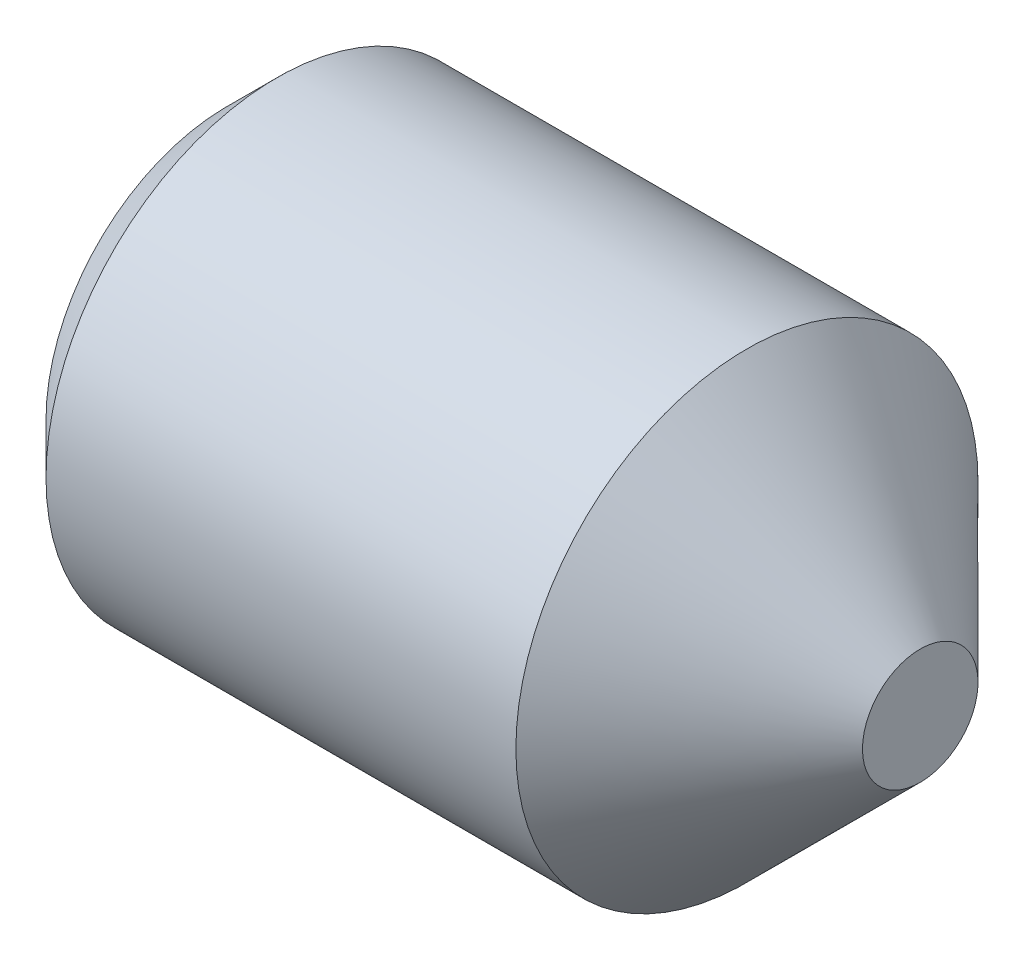
SolidWorks part; units mm, degrees
ref_plane "Front" through (0, 0, 0) normal (0, 0, 1) x (1, 0, 0)
ref_plane "Top" through (0, 0, 0) normal (0, 1, 0) x (1, 0, 0)
ref_plane "Right" through (0, 0, 0) normal (1, 0, 0) x (0, 0, -1)
sketch "Sketch1" plane through (0, 0, 0) normal (0, 0, 1) x (1, 0, 0)
  line L0 (0, 0) -> (3, 0)
  line L1 (3, 0) -> (3, 0.25)
  line L2 (3, 0.25) -> (2.25, 1)
  line L3 (2.25, 1) -> (0.2165, 1)
  line L4 (0.2165, 1) -> (0, 0.7835)
  line L5 (0, 0.7835) -> (0, 0)
  line L6 (-14.7741, 0) -> (12.5137, 0) construction
  dimension "D1" = 45
  dimension "l" = 3
  dimension "D2" = 45
  dimension "dt" = 0.5
  dimension "d" = 2
  dimension "df" = 1.567
revolve "Base" add sketch "Sketch1" angle 360 about L6
cosmetic thread "ThreadCosmetic1" [suppressed] parameters "D2"=1.567
sketch "Sketch2" plane through (0, 0.2203, -0.1392) normal (-1, 0, 0) x (0, 0, 1)
  line L1 (0.6588, -0.2203) -> (0.399, 0.2297)
  line L2 (0.399, 0.2297) -> (-0.1206, 0.2297)
  line L3 (-0.1206, 0.2297) -> (-0.3804, -0.2203)
  line L4 (-0.3804, -0.2203) -> (-0.1206, -0.6703)
  line L5 (-0.1206, -0.6703) -> (0.399, -0.6703)
  line L6 (0.399, -0.6703) -> (0.6588, -0.2203)
  circle A0 centre (0.1392, -0.2203) radius 0.45 construction
  dimension "s" = 0.9
extrude "HexagonSocket" cut sketch "Sketch2" against normal blind 0.8
sketch "Sketch3" plane through (0, 0, 0) normal (0, 0, 1) x (1, 0, 0)
  line L0 (0.8, 0) -> (-2.4777, 0) construction
  line L2 (0.8, 0.45) -> (1.0598, 0)
  line L3 (1.0598, 0) -> (0.8, -0.45) construction
  line L4 (0.8, 0.45) -> (0.8, 0)
  line L5 (0.8, 0) -> (1.0598, 0)
  dimension "D1" = 120
revolve "Cut-Revolve" cut sketch "Sketch3" angle 360 about L0
sketch "Sketch4" plane through (0, 0, 0) normal (0, 0, 1) x (1, 0, 0)
  line L0 (0.2165, 0.8125) -> (0.3248, 1)
  line L1 (0.3248, 1) -> (0.3248, 1.2165)
  line L2 (0.3248, 1.2165) -> (0.1083, 1.2165)
  line L3 (0.1083, 1.2165) -> (0.1083, 1)
  line L4 (0.1083, 1) -> (0.2165, 0.8125)
  line L5 (0, 0) -> (3.2295, 0) construction
  line L6 (0.2165, 1) -> (0.2165, -1) construction
  dimension "D1" = 2
  dimension "D2" = 0.2165
revolve "Cut-Revolve10" [suppressed] cut sketch "Sketch4" angle 360 about L5
pattern_linear "LPattern10" [suppressed] count 12 spacing 0.2598 along (1, 0, 0)
equation "\"df@Sketch1\" = \"D2@ThreadCosmetic1\""
equation "\"D1@Sketch4\" = \"d@Sketch1\""
equation "\"D2@Sketch4\" =  ( \"d@Sketch1\" - \"D2@ThreadCosmetic1\" )  / 2"
equation "\"D3@LPattern10\" = \"D2@Sketch4\" * 1.2"
equation "\"D1@LPattern10\" = \"l@Sketch1\" / \"D3@LPattern10\""
